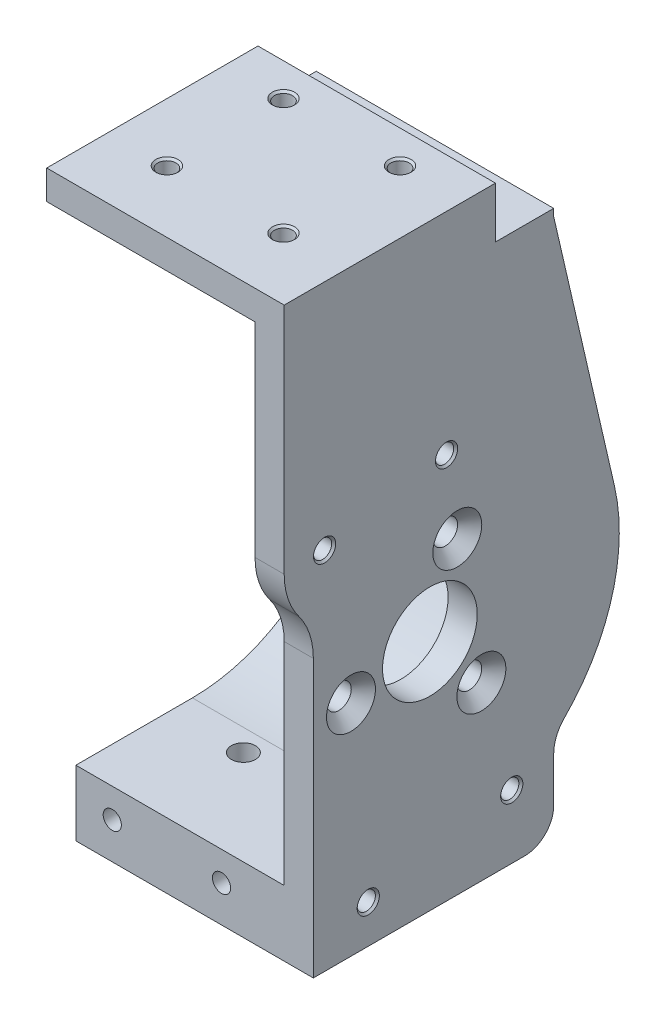
SolidWorks part; units mm, degrees
material "6061 Alloy"
ref_plane "Front Plane" through (0, 0, 0) normal (0, 0, 1) x (1, 0, 0)
ref_plane "Top Plane" through (0, 0, 0) normal (0, 1, 0) x (1, 0, 0)
ref_plane "Right Plane" through (0, 0, 0) normal (1, 0, 0) x (0, 0, -1)
ref_plane "Motor Face w/ 0.5mm tolerance" through (28.6, 0, 0) normal (1, 0, 0) x (0, 0, -1)
sketch "Motor Shell Profile" plane through (0, 0, 0) normal (1, 0, 0) x (0, 0, -1)
  line L0 (25.3355, 5.8404) -> (17, 42)
  line L1 (-16, -32) -> (13, -32)
  line L2 (-20, 46) -> (-20, 50)
  line L3 (-20, 50) -> (17, 50)
  line L4 (17, -21.8403) -> (17, -28)
  line L5 (0, -22) -> (-16, -22)
  line L6 (-16, -22) -> (-16, -32)
  line L7 (17, 42) -> (17, 50)
  line L8 (10.8951, 46) -> (-20, 46)
  line L9 (12.8951, 44) -> (12.8951, 42)
  line L10 (12.8951, 42) -> (21.4378, 4.9419)
  arc A0 (0, -22) -> (21.4378, 4.9419) centre (0, 0) ccw
  arc A1 (18.4516, -18.3177) -> (25.3355, 5.8404) centre (0, 0) ccw
  arc A2 (17, -21.8403) -> (18.4516, -18.3177) centre (22, -21.8403) cw
  arc A3 (13, -32) -> (17, -28) centre (13, -28) ccw
  arc A4 (12.8951, 44) -> (10.8951, 46) centre (10.8951, 44) ccw
  point P17 (17, -32)
  dimension "D1" = 4
  dimension "Motor Diameter" = 22
  dimension "D3" = 26
  dimension "D6" = 5
  dimension "D7" = 4
  dimension "D11" = 2
  dimension "D2" = 10
  dimension "D4" = 16
  dimension "D5" = 33
  dimension "D8" = 20
  dimension "D9" = 50
  dimension "D10" = 8
extrude "Motor Shell" add sketch "Motor Shell Profile" along normal offset from surface (32.6 mm away) 4 up to plane "Motor Face w/ 0.5mm tolerance" offset beyond the face yes
sketch "Sketch3" plane through (28.6, 0, 0) normal (1, 0, 0) x (0, 0, -1)
  line L0 (-20, 46) -> (12.8951, 46)
  line L1 (-16, -22) -> (0, -22)
  line L2 (-16, -22) -> (-16, 6)
  line L3 (21.4378, 4.9419) -> (12.8951, 42)
  line L4 (-20, 18) -> (-20, 46)
  line L5 (12.8951, 42) -> (12.8951, 46)
  arc A0 (21.4378, 4.9419) -> (0, -22) centre (0, 0) cw
  arc A1 (-18, 12) -> (-20, 18) centre (-10, 18) cw
  circle A2 centre (0, 0) radius 11 construction
  arc A3 (0, -22) -> (21.4378, 4.9419) centre (0, 0) ccw construction
  arc A4 (-16, 6) -> (-18, 12) centre (-26, 6) ccw
  dimension "D1" = 22
  dimension "D2" = 10
  dimension "D4" = 18
extrude "Motor Mount" add sketch "Sketch3" along normal blind 4
hole_wizard "Mounting Hole" positions "Sketch9" profile "Sketch10" countersink size "M3" standard "ANSI Metric" end condition through all
sketch "Sketch9" plane through (32.6, 0, 0) normal (1, 0, 0) x (0, 0, -1)
  line L2 (-6.2562, 0) -> (26, 0) construction
  line L5 (0, 0) -> (11.7452, -13.9973) construction
  arc A0 (18.4516, -18.3177) -> (25.3355, 5.8404) centre (0, 0) ccw construction
  point P0 (7.0707, -8.4265)
  dimension "D1" = 50
  dimension "D2" = 11
sketch "Sketch10" plane through (32.6, -8.4265, -7.0707) normal (0, 1, 0) x (0, 0, -1)
  line L0 (0, 0) -> (0, 32.6)
  line L1 (0, 32.6) -> (1.7, 32.6)
  line L2 (1.7, 32.6) -> (1.7, 1.66)
  line L3 (1.7, 1.66) -> (3.36, 0)
  line L5 (3.36, 0) -> (0, 0)
  line L6 (-1.7, 1.66) -> (-3.36, 0) construction
  line L11 (0, -6.35) -> (0, 107.95) construction
  dimension "Thru Hole Dia." = 3.4
  dimension "Thru Hole Depth" = 32.6
  dimension "Near C'Sink Dia." = 6.72
  dimension "Near C'Sink Angle" = 90
pattern_circular "Hole Duplication" count 3 over 360 about axis through (0, 0, 0) along (1, 0, 0) of "Mounting Hole"
sketch "Sketch11" plane through (32.6, 0, 0) normal (1, 0, 0) x (0, 0, -1)
  circle A0 centre (0, 0) radius 6.5
  dimension "D1" = 13
extrude "Shaft Base Cutout" cut sketch "Sketch11" against normal through all
ref_plane "U Joint Base Plane" through (35.1, 0, 0) normal (1, 0, 0) x (0, 0, -1)
ref_plane "Pin Hole Plane" through (0, 0, 15) normal (0, 0, 1) x (1, 0, 0)
hole_wizard "M3x0.5 Tapped Hole1" positions "Sketch13" profile "Sketch15" tap size "M3x0.5" standard "ANSI Metric"
sketch "Sketch13" plane through (32.6, 0, 0) normal (1, 0, 0) x (0, 0, -1)
  line L0 (-8.4589, -26.7365) -> (11.2373, -23.2635) construction
  line L2 (-8.4589, -26.7365) -> (-9.8481, -18.858) construction
  line L3 (-9.8481, -18.858) -> (9.8481, -15.3851) construction
  line L5 (9.8481, -15.3851) -> (11.2373, -23.2635) construction
  line L6 (-16, -32) -> (13, -32) construction
  line L7 (-14.4522, 18.0982) -> (-12.8025, 8.7426) construction
  line L8 (-12.8025, 8.7426) -> (3.9392, 11.6946) construction
  line L9 (3.9392, 11.6946) -> (2.2896, 21.0503) construction
  line L11 (-14.4522, 18.0982) -> (2.2896, 21.0503) construction
  line L12 (-8.8633, 9.4372) -> (0, 11) construction
  point P0 (-8.4589, -26.7365)
  point P2 (11.2373, -23.2635)
  point P9 (-14.4522, 18.0982)
  point P11 (2.2896, 21.0503)
  point P34 (0, -17.1215)
  point P36 (1.3892, -25)
  point P69 (-4.4316, 10.2186)
  dimension "D1" = 20
  dimension "D2" = 8
  dimension "D3" = 25
  dimension "D4" = 9.5
  dimension "D5" = 17
  dimension "D6" = 4.5
  dimension "D7" = 10
  dimension "D8" = 4.5
  dimension "D9" = 11
sketch "Sketch15" plane through (32.6, -26.7365, 8.4589) normal (0, 1, 0) x (0, 0, -1)
  line L0 (0, 0) -> (0, 10.7511)
  line L1 (0, 10.7511) -> (1.25, 10)
  line L2 (1.25, 10) -> (1.25, 0.275)
  line L3 (1.25, 0.275) -> (1.525, 0)
  line L5 (1.525, 0) -> (0, 0)
  line L6 (-1.25, 0.275) -> (-1.525, 0) construction
  line L10 (0, 10.7511) -> (-1.25, 10) construction
  line L11 (0, -6.35) -> (0, 107.95) construction
  dimension "Tap Drill Dia." = 2.5
  dimension "Tap Drill Depth" = 10
  dimension "Near C'Sink Dia." = 3.05
  dimension "Near C'Sink Angle" = 90
  dimension "Drill Angle" = 118
sketch "Sketch16" plane through (32.6, 0, 0) normal (1, 0, 0) x (0, 0, -1)
  line L0 (-17, -32) -> (-17, -16)
  line L1 (-16, -32) -> (13, -32) construction
  line L2 (-17, -16) -> (20.4939, -16)
  line L3 (20.4939, -16) -> (20.4939, -32)
  line L4 (20.4939, -32) -> (-17, -32)
  line L5 (17, -28) -> (17, -21.8403) construction
  arc A0 (18.4516, -18.3177) -> (25.3355, 5.8404) centre (0, 0) ccw construction
  point P14 (17, -24.9202)
  dimension "D1" = 16
  dimension "D2" = 34
extrude "Pin Mount Recess" [suppressed] cut sketch "Sketch16" against normal blind 2
hole_wizard "M3x0.5 Tapped Hole2" positions "Sketch17" profile "Sketch18" tap size "M3x0.5" standard "ANSI Metric"
sketch "Sketch17" plane through (0, 50, 0) normal (0, 1, 0) x (1, 0, 0)
  line L2 (16, 17) -> (16, -20) construction
  line L6 (0, -1.5) -> (43.0377, -1.5) construction
  line L7 (0, 17) -> (0, -20) construction
  line L8 (0, 17) -> (0, -20) construction
  point P2 (8, 4.5)
  point P23 (8, -11.5)
  point P29 (24, -11.5)
  point P31 (24, 4.5)
  dimension "D1" = 16
  dimension "D2" = 8
  dimension "D3" = 6
  dimension "D4" = 10
  dimension "D5" = 16
sketch "Sketch18" plane through (8, 50, -4.5) normal (1, 0, 0) x (0, 0, 1)
  line L0 (0, 0) -> (0, 8.2511)
  line L1 (0, 8.2511) -> (1.25, 7.5)
  line L2 (1.25, 7.5) -> (1.25, 0.275)
  line L3 (1.25, 0.275) -> (1.525, 0)
  line L5 (1.525, 0) -> (0, 0)
  line L6 (-1.25, 0.275) -> (-1.525, 0) construction
  line L10 (0, 8.2511) -> (-1.25, 7.5) construction
  line L11 (0, -6.35) -> (0, 107.95) construction
  dimension "Tap Drill Dia." = 2.5
  dimension "Tap Drill Depth" = 7.5
  dimension "Near C'Sink Dia." = 3.05
  dimension "Near C'Sink Angle" = 90
  dimension "Drill Angle" = 118
cosmetic thread "Hole Thread1" parameters "D1"=4, "D2"=3
cosmetic thread "Hole Thread3" parameters "D1"=4, "D2"=3
cosmetic thread "Hole Thread7" parameters "D1"=4, "D2"=3
cosmetic thread "Hole Thread8" parameters "D1"=4, "D2"=3
hole_wizard "M3x0.5 Tapped Hole5" positions "Sketch25" profile "Sketch24" tap size "M3x0.5" standard "ANSI Metric"
sketch "Sketch25" plane through (0, 0, 16) normal (0, 0, 1) x (1, 0, 0)
  line L1 (0, -22) -> (0, -32) construction
  line L2 (32.6, -32) -> (0, -32) construction
  point P0 (5, -27)
  point P2 (20, -27)
  dimension "D1" = 15
  dimension "D2" = 5
  dimension "D3" = 5
cosmetic thread "Hole Thread5" parameters "D1"=2.4, "D2"=3
cosmetic thread "Hole Thread6" parameters "D1"=2.4, "D2"=3
sketch "Sketch24" plane through (5, -27, 16) normal (1, 0, 0) x (0, -1, 0)
  line L0 (0, 0) -> (0, 10.7511)
  line L1 (0, 10.7511) -> (1.25, 10)
  line L2 (1.25, 10) -> (1.25, 0)
  line L5 (1.25, 0) -> (0, 0)
  line L10 (0, 10.7511) -> (-1.25, 10) construction
  line L11 (0, -6.35) -> (0, 107.95) construction
  dimension "Tap Drill Dia." = 2.5
  dimension "Tap Drill Depth" = 10
  dimension "Drill Angle" = 118
sketch "Sketch26" plane through (0, 0, -17) normal (0, 0, -1) x (-1, 0, 0)
  line L0 (-32.6, 50) -> (0, 50) construction
  line L1 (0, 42) -> (0, 50) construction
  circle A1 centre (-10, 25.75) radius 1.35
  dimension "D3" = 2.7
  dimension "D1" = 24.25
  dimension "D2" = 10
extrude "M3x0.5 Tapped Hole6" cut sketch "Sketch26" against normal up to next and the other way up to next
hole_wizard "M4x0.7 Tapped Hole1" positions "Sketch27" profile "Sketch28" tap size "M4x0.7" standard "ANSI Metric"
sketch "Sketch27" plane through (0, -32, 0) normal (0, -1, 0) x (-1, 0, 0)
  line L0 (0, -16) -> (0, 13) construction
  line L1 (-32.6, -16) -> (0, -16) construction
  point P0 (-10, -3)
  dimension "D1" = 10
  dimension "D2" = 13
sketch "Sketch28" plane through (10, -32, 3) normal (1, 0, 0) x (0, 0, -1)
  line L0 (0, 0) -> (0, 12.4914)
  line L1 (0, 12.4914) -> (1.65, 11.5)
  line L2 (1.65, 11.5) -> (1.65, 0)
  line L5 (1.65, 0) -> (0, 0)
  line L10 (0, 12.4914) -> (-1.65, 11.5) construction
  line L11 (0, -6.35) -> (0, 107.95) construction
  dimension "Tap Drill Dia." = 3.3
  dimension "Tap Drill Depth" = 11.5
  dimension "Drill Angle" = 118
cosmetic thread "Hole Thread9" parameters "D1"=8, "D2"=4
sketch "Sketch29" plane through (0, 0, 0) normal (-1, 0, 0) x (0, 0, 1)
  line L0 (0, -23) -> (16, -23)
  line L1 (16, -22) -> (16, -32) construction
  line L2 (-22.4122, 5.1665) -> (-13.9213, 42)
  line L3 (-12.8951, 42) -> (-21.4378, 4.9419) construction
  line L4 (-13.9213, 42) -> (-13.9213, 44)
  line L5 (20, 46) -> (-11.9213, 46)
  line L6 (20, 46) -> (20, 18) construction
  line L7 (16, 6) -> (16, -22) construction
  line L8 (20, 46) -> (20, 18)
  line L9 (16, 6) -> (16, -23)
  arc A0 (-22.4122, 5.1665) -> (0, -23) centre (0, 0) ccw
  arc A4 (18, 12) -> (20, 18) centre (10, 18) ccw construction
  arc A5 (18, 12) -> (16, 6) centre (26, 6) ccw construction
  arc A6 (18, 12) -> (20, 18) centre (10, 18) ccw
  arc A7 (18, 12) -> (16, 6) centre (26, 6) ccw
  arc A8 (-11.9213, 46) -> (-13.9213, 44) centre (-11.9213, 44) ccw
  dimension "D1" = 46
  dimension "D2" = 2
extrude "Enlarge Cavity" cut sketch "Sketch29" against normal up to surface (28.6 mm away) up to face at (28.6, 18.0982, 15.7022)
sketch "Sketch30" plane through (0, 0, 0) normal (-1, 0, 0) x (0, 0, 1)
  line L0 (-16.4571, 31) -> (3, 42)
  line L1 (-22.4122, 5.1665) -> (-13.9213, 42) construction
  line L2 (3, 42) -> (3, 46)
  line L3 (20, 46) -> (-11.9213, 46) construction
  line L4 (-13.9213, 44) -> (-13.9213, 42) construction
  line L5 (3, 46) -> (-11.9213, 46)
  line L6 (-13.9213, 44) -> (-13.9213, 42)
  line L7 (-16.4571, 31) -> (-13.9213, 42)
  line L8 (-17, 42) -> (-17, 50) construction
  line L9 (-17, 50) -> (20, 50) construction
  arc A0 (-11.9213, 46) -> (-13.9213, 44) centre (-11.9213, 44) ccw construction
  arc A1 (-11.9213, 46) -> (-13.9213, 44) centre (-11.9213, 44) ccw
  point P11 (3, 41.1527)
  dimension "D1" = 20
  dimension "D2" = 15
  dimension "D3" = 8
extrude "Mod 1" add sketch "Sketch30" against normal up to surface (28.6 mm away) up to face at (28.6, 16.8177, 2.0618)
sketch "Sketch31" plane through (0, 0, 0) normal (-1, 0, 0) x (0, 0, 1)
  line L1 (-17, 50) -> (-9, 50)
  line L2 (-17, 50) -> (-17, 43)
  line L3 (-17, 43) -> (-9, 43)
  line L4 (-9, 50) -> (-9, 43)
  dimension "D1" = 8
  dimension "D2" = 7
extrude "Mod 2" cut sketch "Sketch31" against normal up to surface (32.6 mm away) up to face at (32.6, -26.7365, 6.9339)
hole_wizard "Hole1" positions "Sketch34" profile "Sketch33" legacy
sketch "Sketch34" plane through (0, 0, -9) normal (0, 0, -1) x (-1, 0, 0)
  line L0 (-32.6, 43) -> (0, 43) construction
  line L1 (0, 43) -> (0, 50) construction
  point P0 (-17.5, 46.5)
  dimension "D1" = 3.5
  dimension "D2" = 17.5
sketch "Sketch33" plane through (17.5, 46.5, -9) normal (1, 0, 0) x (0, 1, 0)
  line L0 (0, 0) -> (0, 3.8)
  line L1 (0, 3.8) -> (2.55, 3.8)
  line L2 (2.55, 3.8) -> (2.55, 1.5257)
  line L3 (2.55, 1.5257) -> (2.65, 0)
  line L4 (2.65, 0) -> (0, 0)
  line L5 (0, -6.4453) -> (0, 115.525) construction
  line L6 (-2.55, 1.5257) -> (-2.65, 0) construction
  dimension "Diameter" = 5.1
  dimension "Depth" = 3.8
  dimension "C-Sink Angle" = 7.5
  dimension "C-Sink Diameter" = 5.3
